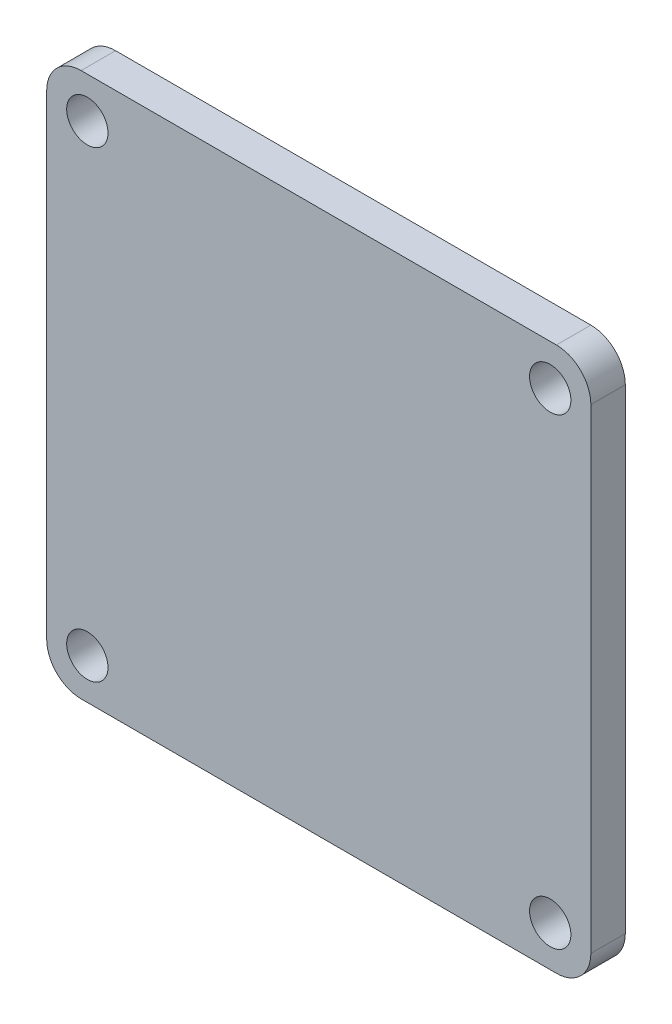
SolidWorks part; units mm, degrees
ref_plane "Front Plane" through (0, 0, 0) normal (0, 0, 1) x (1, 0, 0)
ref_plane "Top Plane" through (0, 0, 0) normal (0, 1, 0) x (1, 0, 0)
ref_plane "Right Plane" through (0, 0, 0) normal (1, 0, 0) x (0, 0, -1)
sketch "Sketch1" plane through (0, 0, 0) normal (0, 0, 1) x (1, 0, 0)
  line L1 (0, 0) -> (39.5, 0)
  line L2 (0, 0) -> (0, 39.5)
  line L3 (0, 39.5) -> (39.5, 39.5)
  line L4 (39.5, 0) -> (39.5, 39.5)
  dimension "D1" = 39.5
  dimension "D2" = 39.5
extrude "Boss-Extrude1" add sketch "Sketch1" along normal blind 2.5
sketch "Sketch2" plane through (0, 0, 2.5) normal (0, 0, 1) x (1, 0, 0)
  line L0 (39.5, 39.5) -> (0, 39.5) construction
  line L1 (0, 39.5) -> (0, 0) construction
  line L2 (0, 0) -> (39.5, 0) construction
  line L3 (39.5, 0) -> (39.5, 39.5) construction
  circle A0 centre (2.95, 36.55) radius 1.5
  circle A1 centre (36.55, 36.55) radius 1.5
  circle A2 centre (36.55, 2.95) radius 1.5
  circle A3 centre (2.95, 2.95) radius 1.5
  dimension "D5" = 3
  dimension "D6" = 3
  dimension "D7" = 3
  dimension "D8" = 2.95
  dimension "D12" = 3
  dimension "D1" = 2.95
  dimension "D2" = 2.95
  dimension "D3" = 2.95
  dimension "D4" = 2.95
  dimension "D9" = 2.95
  dimension "D10" = 2.95
  dimension "D11" = 2.95
extrude "Cut-Extrude1" cut sketch "Sketch2" against normal blind 2.5
fillet "Fillet1" radius 2.5 4 edges at (0, 0, 1.25) (39.5, 0, 1.25) (39.5, 39.5, 1.25) (0, 39.5, 1.25)
